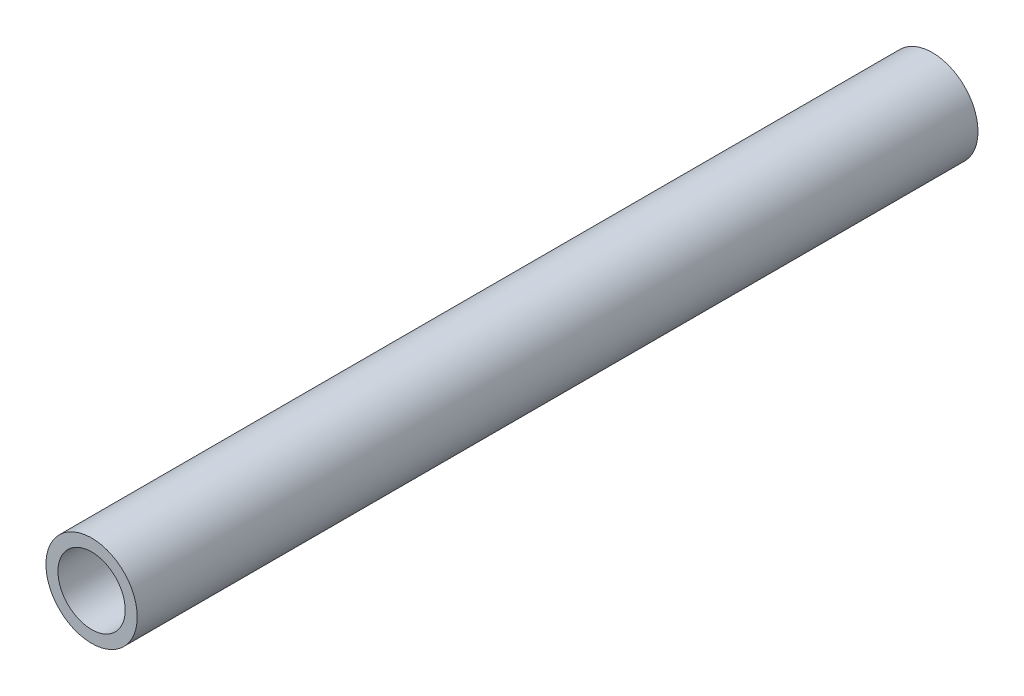
SolidWorks part; units mm, degrees
ref_plane "Front Plane" through (0, 0, 0) normal (0, 0, 1) x (1, 0, 0)
ref_plane "Top Plane" through (0, 0, 0) normal (0, 1, 0) x (1, 0, 0)
ref_plane "Right Plane" through (0, 0, 0) normal (1, 0, 0) x (0, 0, -1)
sketch "Sketch1" plane through (0, 0, 0) normal (0, 0, 1) x (1, 0, 0)
  circle A0 centre (0, 0) radius 4.826
  circle A1 centre (0, 0) radius 3.556
  dimension "D1" = 7.112
  dimension "D2" = 1.27
extrude "Boss-Extrude1" add sketch "Sketch1" along normal blind 88.8746
